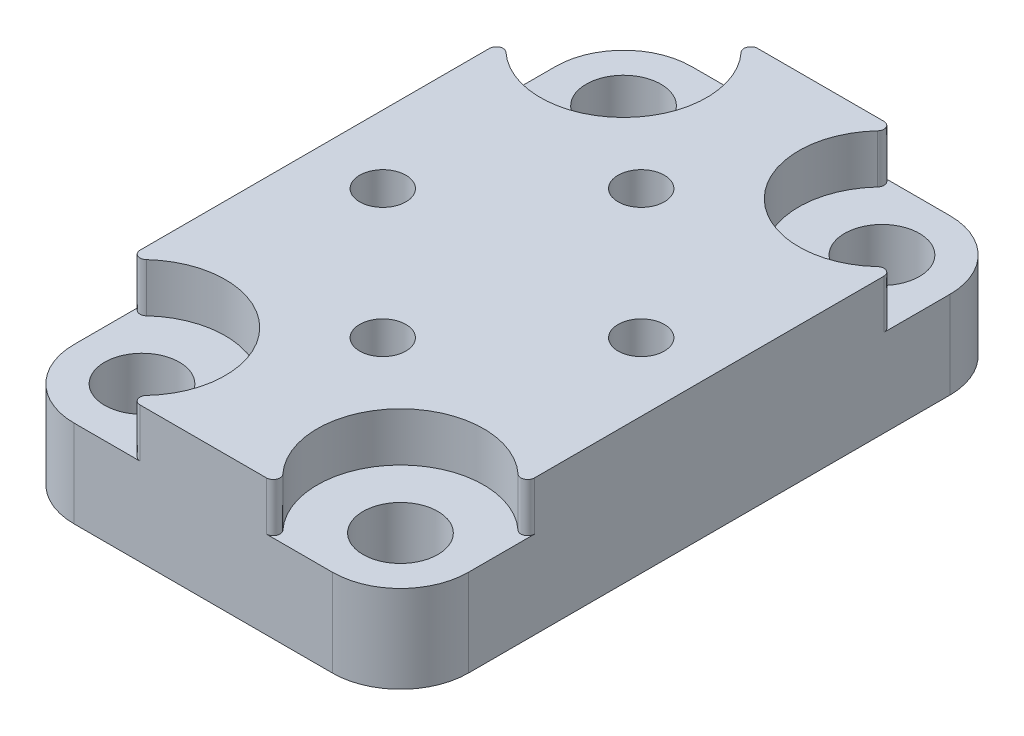
SolidWorks part; units mm, degrees
material "1060 Alloy"
ref_plane "Front Plane" through (0, 0, 0) normal (0, 0, 1) x (1, 0, 0)
ref_plane "Top Plane" through (0, 0, 0) normal (0, 1, 0) x (1, 0, 0)
ref_plane "Right Plane" through (0, 0, 0) normal (1, 0, 0) x (0, 0, -1)
sketch "Sketch1" plane through (0, 0, 0) normal (0, 1, 0) x (1, 0, 0)
  line L0 (0, 9.5) -> (0, 0) construction
  line L1 (0, 0) -> (9.5, 0) construction
  line L2 (-9.5, 17.7) -> (9.5, 17.7) construction
  line L3 (-9.5, -17.7) -> (9.5, -17.7) construction
  line L4 (-14.5, 22.7) -> (14.5, 22.7)
  line L5 (14.5, 22.7) -> (14.5, -22.7)
  line L6 (-14.5, 22.7) -> (-14.5, -22.7)
  line L7 (-14.5, -22.7) -> (14.5, -22.7)
  circle A0 centre (-9.5, 17.7) radius 2.5 construction
  circle A1 centre (9.5, 17.7) radius 2.5 construction
  circle A2 centre (9.5, -17.7) radius 2.5 construction
  circle A3 centre (-9.5, -17.7) radius 2.5 construction
  point P3 (-9.5, 17.7)
  point P5 (0, 9.5)
  point P6 (9.5, 0)
  point P7 (0, -9.5)
  point P8 (-9.5, 0)
  point P12 (9.5, 17.7)
  point P27 (0, 22.7)
  point P28 (-14.5, 0)
  point P29 (14.5, 0)
  dimension "D2" = 5
  dimension "D4" = 2.5
  dimension "D5" = 2.5
  dimension "D1" = 19
  dimension "D3" = 35.4
extrude "Boss-Extrude1" add sketch "Sketch1" against normal blind 10
hole_wizard "CBORE for M5 Hex Head Bolt1" positions "Sketch2" profile "Sketch3" counterbore size "M5" standard "ANSI Metric"
sketch "Sketch2" plane through (0, 0, 0) normal (0, 1, 0) x (1, 0, 0)
  point P0 (-9.5, 17.7)
  point P3 (9.5, 17.7)
  point P6 (9.5, -17.7)
  point P9 (-9.5, -17.7)
sketch "Sketch3" plane through (-9.5, 0, -17.7) normal (1, 0, 0) x (0, 0, 1)
  line L0 (0, 0) -> (0, 16.6524)
  line L1 (0, 16.6524) -> (2.75, 15)
  line L2 (2.75, 15) -> (2.75, 3.58)
  line L3 (2.75, 3.58) -> (6.12, 3.58)
  line L4 (6.12, 3.58) -> (6.12, 0)
  line L5 (6.12, 0) -> (0, 0)
  line L10 (0, 16.6524) -> (-2.75, 15) construction
  line L11 (0, -6.35) -> (0, 107.95) construction
  dimension "Hole Dia." = 5.5
  dimension "Hole Depth" = 15
  dimension "C'Bore Dia." = 12.24
  dimension "C'Bore Depth" = 3.58
  dimension "Drill Angle" = 118
hole_wizard "CSK for M3 Flat Head Machine Screw1" positions "Sketch4" profile "Sketch6" countersink size "M3" standard "ANSI Metric" end condition through all
sketch "Sketch4" plane through (0, -10, 0) normal (0, -1, 0) x (-1, 0, 0)
  point P0 (-9.5, 0)
  point P3 (0, 9.5)
  point P6 (9.5, 0)
  point P9 (0, -9.5)
sketch "Sketch6" plane through (9.5, -10, 0) normal (1, 0, 0) x (0, 0, -1)
  line L0 (0, 0) -> (0, 10)
  line L1 (0, 10) -> (1.7, 10)
  line L2 (1.7, 10) -> (1.7, 1.45)
  line L3 (1.7, 1.45) -> (3.15, 0)
  line L5 (3.15, 0) -> (0, 0)
  line L6 (-1.7, 1.45) -> (-3.15, 0) construction
  line L11 (0, -6.35) -> (0, 107.95) construction
  dimension "Thru Hole Dia." = 3.4
  dimension "Thru Hole Depth" = 10
  dimension "Near C'Sink Dia." = 6.3
  dimension "Near C'Sink Angle" = 90
fillet "Fillet1" radius 5 4 edges at (-14.5, -5, -22.7) (14.5, -5, -22.7) (14.5, -5, 22.7) (-14.5, -5, 22.7)
fillet "Fillet2" radius 0.5 8 edges at (-14.5, -1.79, -14.1709) (-5.9709, -1.79, -22.7) (5.9709, -1.79, -22.7) (14.5, -1.79, -14.1709) (14.5, -1.79, 14.1709) (5.9709, -1.79, 22.7) (-5.9709, -1.79, 22.7) (-14.5, -1.79, 14.1709)
